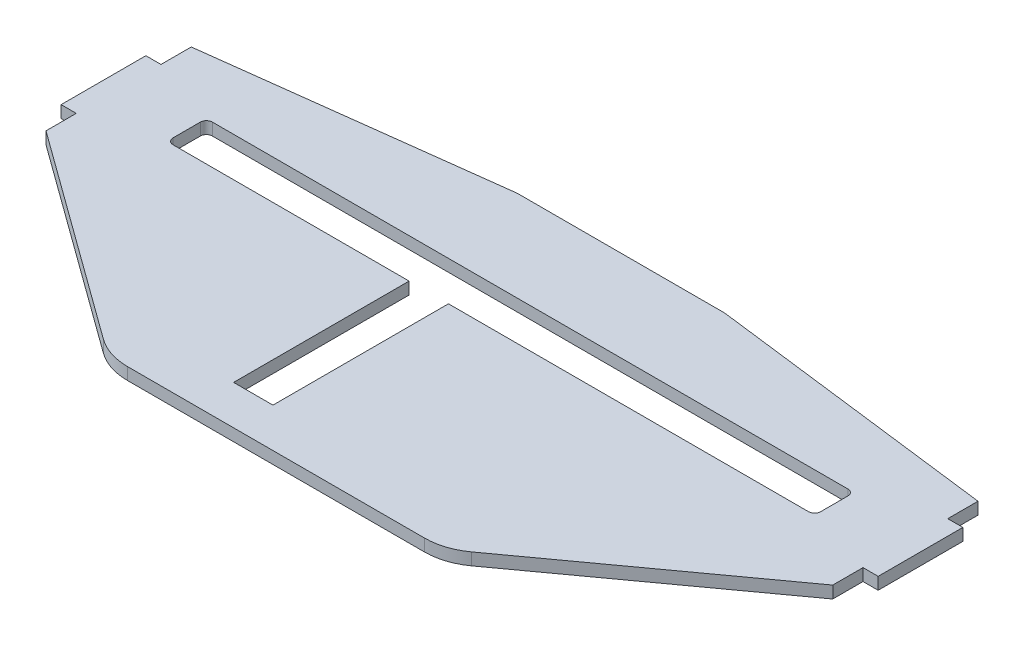
SolidWorks part; units mm, degrees
material "Plástico personalizado"
ref_plane "Plano frontal" through (0, 0, 0) normal (0, 0, 1) x (1, 0, 0)
ref_plane "Plano superior" through (0, 0, 0) normal (0, 1, 0) x (1, 0, 0)
ref_plane "Plano direito" through (0, 0, 0) normal (1, 0, 0) x (0, 0, -1)
sketch "Esboço1" plane through (0, 0, 0) normal (0, 1, 0) x (1, 0, 0)
  line L0 (-65, 27.6905) -> (-17.7746, 33.6128)
  line L1 (-16.5303, 33.6905) -> (0, 33.6905)
  line L2 (0, -23.3095) -> (0, 33.6905)
  line L9 (0, -23.3095) -> (-24.5413, -23.3095)
  line L10 (-30.4139, -21.4035) -> (-65, 3.6905)
  line L11 (-65, 3.6905) -> (-65, 8.6905)
  line L12 (-65, 8.6905) -> (-67.5, 8.6905)
  line L13 (-67.5, 8.6905) -> (-67.5, 22.6905)
  line L14 (-67.5, 22.6905) -> (-65, 22.6905)
  line L15 (-65, 22.6905) -> (-65, 27.6905)
  arc A0 (-16.5303, 33.6905) -> (-17.7746, 33.6128) centre (-16.5303, 23.6905) ccw
  arc A1 (-24.5413, -23.3095) -> (-30.4139, -21.4035) centre (-24.5413, -13.3095) cw
  point P6 (-17.1549, 33.6905)
  dimension "D1" = 10
  dimension "D6" = 67.5
  dimension "D2" = 6
  dimension "D3" = 57
  dimension "D4" = 2.5
  dimension "D5" = 24
  dimension "D7" = 5
extrude "Ressalto-extrusão1" add sketch "Esboço1" along normal blind 2
mirror "Espelhar1" about plane through (0, 2, 23.3095) normal (-1, 0, 0) of "Ressalto-extrusão1"
sketch "Esboço2" plane through (0, 2, 0) normal (0, 1, 0) x (1, 0, 0)
  line L0 (16.5303, 33.6905) -> (-16.5303, 33.6905) construction
  line L1 (-52.5, 18.6905) -> (52.5, 18.6905)
  line L2 (-53.5, 17.6905) -> (-53.5, 13.1905)
  line L3 (-52.5, 12.1905) -> (-13.5, 12.1905)
  line L4 (53.5, 17.6905) -> (53.5, 13.1905)
  line L5 (-53.5, 18.6905) -> (53.5, 12.1905) construction
  line L6 (-53.5, 12.1905) -> (53.5, 18.6905) construction
  line L7 (67.5, 22.6905) -> (67.5, 8.6905) construction
  line L8 (-7, 12.1905) -> (52.5, 12.1905)
  line L9 (-13.5, -16.8095) -> (-7, -16.8095)
  line L10 (-13.5, -16.8095) -> (-13.5, 12.1905)
  line L12 (-7, -16.8095) -> (-7, 12.1905)
  line L13 (-13.5, -16.8095) -> (-7, 12.1905) construction
  line L14 (-13.5, 12.1905) -> (-7, -16.8095) construction
  arc A0 (53.5, 13.1905) -> (52.5, 12.1905) centre (52.5, 13.1905) cw
  arc A1 (53.5, 17.6905) -> (52.5, 18.6905) centre (52.5, 17.6905) ccw
  arc A2 (-53.5, 17.6905) -> (-52.5, 18.6905) centre (-52.5, 17.6905) cw
  arc A3 (-53.5, 13.1905) -> (-52.5, 12.1905) centre (-52.5, 13.1905) ccw
  point P0 (0, 15.4405)
  point P21 (-10.25, -2.3095)
  dimension "D4" = 1
  dimension "D1" = 107
  dimension "D2" = 15
  dimension "D3" = 14
  dimension "D5" = 40
  dimension "D6" = 6.5
  dimension "D7" = 6.5
  dimension "D8" = 29
extrude "Corte-extrusão1" cut sketch "Esboço2" against normal through all
